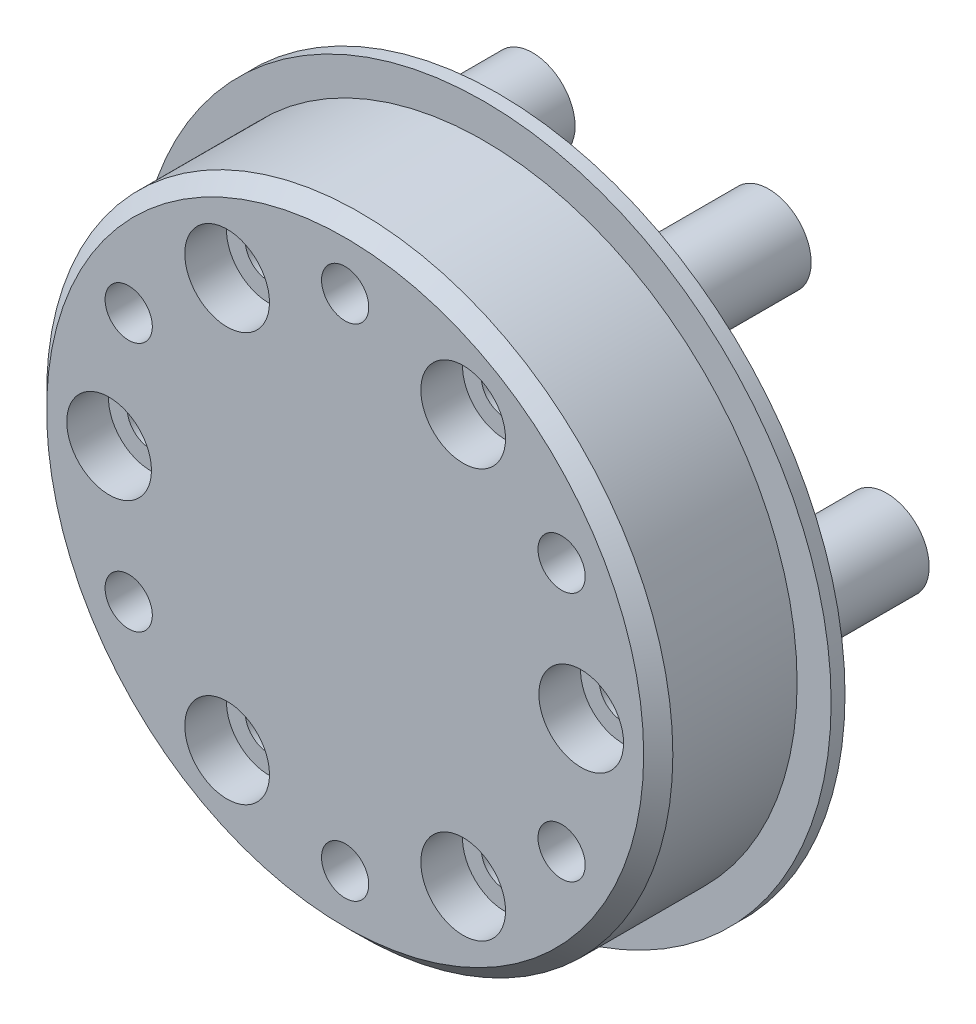
SolidWorks part; units mm, degrees
ref_plane "前视基准面" through (0, 0, 0) normal (0, 0, 1) x (1, 0, 0)
ref_plane "上视基准面" through (0, 0, 0) normal (0, 1, 0) x (1, 0, 0)
ref_plane "右视基准面" through (0, 0, 0) normal (1, 0, 0) x (0, 0, -1)
sketch "草图1" plane through (0, 0, 0) normal (0, 1, 0) x (1, 0, 0)
  line L0 (25, 11) -> (0, 11)
  line L1 (0, 11) -> (0, 10)
  line L2 (0, 10) -> (25, 10)
  line L3 (25, 10) -> (25, 11)
  line L4 (0, 11) -> (0, 10) construction
revolve "旋转1" add sketch "草图1" angle 360 about L4
sketch "草图2" plane through (0, 0, -10) normal (0, 0, 1) x (1, 0, 0)
  circle A0 centre (0, 0) radius 22.55
extrude "凸台-拉伸1" add sketch "草图2" along normal blind 10
ref_plane "基准面4" through (0, -14.7224, 0) normal (0, 1, 0) x (1, 0, 0)
sketch "草图3" plane through (0, -14.7224, 0) normal (0, 1, 0) x (1, 0, 0)
  line L0 (11.56, 22) -> (8.5, 22)
  line L1 (8.5, 22) -> (8.5, 11)
  line L2 (8.5, 11) -> (12.5, 11)
  line L3 (12.5, 11) -> (12.5, 12.5)
  line L4 (12.5, 12.5) -> (11.56, 12.5)
  line L5 (11.56, 12.5) -> (11.56, 22)
  line L6 (8.5, 22) -> (8.5, 11) construction
revolve "旋转2" add sketch "草图3" angle 360 about L6
sketch "草图4" plane through (0, -14.7224, 0) normal (0, 1, 0) x (1, 0, 0)
  line L0 (-5.44, 22) -> (-8.5, 22)
  line L1 (-8.5, 22) -> (-8.5, 11)
  line L2 (-8.5, 11) -> (-4.5, 11)
  line L3 (-4.5, 11) -> (-4.5, 12.5)
  line L4 (-4.5, 12.5) -> (-5.44, 12.5)
  line L5 (-5.44, 12.5) -> (-5.44, 22)
  line L6 (-8.5, 22) -> (-8.5, 11) construction
revolve "旋转3" add sketch "草图4" angle 360 about L6
sketch "草图5" plane through (0, 0, 0) normal (0, 1, 0) x (1, 0, 0)
  line L0 (-13.94, 22) -> (-17, 22)
  line L1 (-17, 22) -> (-17, 11)
  line L2 (-17, 11) -> (-13, 11)
  line L3 (-13, 11) -> (-13, 12.5)
  line L4 (-13, 12.5) -> (-13.94, 12.5)
  line L5 (-13.94, 12.5) -> (-13.94, 22)
  line L6 (-17, 22) -> (-17, 11) construction
revolve "旋转4" add sketch "草图5" angle 360 about L6
ref_plane "基准面5" through (0, 14.7224, 0) normal (0, 1, 0) x (1, 0, 0)
sketch "草图6" plane through (0, 14.7224, 0) normal (0, 1, 0) x (1, 0, 0)
  line L0 (-5.44, 22) -> (-8.5, 22)
  line L1 (-8.5, 22) -> (-8.5, 11)
  line L2 (-8.5, 11) -> (-4.5, 11)
  line L3 (-4.5, 11) -> (-4.5, 12.5)
  line L4 (-4.5, 12.5) -> (-5.44, 12.5)
  line L5 (-5.44, 12.5) -> (-5.44, 22)
  line L6 (-8.5, 22) -> (-8.5, 11) construction
revolve "旋转5" add sketch "草图6" angle 360 about L6
sketch "草图7" plane through (0, 14.7224, 0) normal (0, 1, 0) x (1, 0, 0)
  line L0 (11.56, 22) -> (8.5, 22)
  line L1 (8.5, 22) -> (8.5, 11)
  line L2 (8.5, 11) -> (12.5, 11)
  line L3 (12.5, 11) -> (12.5, 12.5)
  line L4 (12.5, 12.5) -> (11.56, 12.5)
  line L5 (11.56, 12.5) -> (11.56, 22)
  line L6 (8.5, 22) -> (8.5, 11) construction
revolve "旋转6" add sketch "草图7" angle 360 about L6
sketch "草图8" plane through (0, 0, 0) normal (0, 1, 0) x (1, 0, 0)
  line L0 (20.06, 22) -> (17, 22)
  line L1 (17, 22) -> (17, 11)
  line L2 (17, 11) -> (21, 11)
  line L3 (21, 11) -> (21, 12.5)
  line L4 (21, 12.5) -> (20.06, 12.5)
  line L5 (20.06, 12.5) -> (20.06, 22)
  line L6 (17, 22) -> (17, 11) construction
revolve "旋转7" add sketch "草图8" angle 360 about L6
hole_wizard "M3 六角头机械螺钉的柱形沉头孔1" positions "草图10" profile "草图9" counterbore size "M3" standard "ANSI Metric"
sketch "草图10" plane through (0, 0, -11) normal (0, 0, -1) x (-1, 0, 0)
  point P0 (15.5885, 9)
  point P1 (0, 18)
  point P2 (-15.5885, 9)
  point P3 (-15.5885, -9)
  point P4 (0, -18)
  point P5 (15.5885, -9)
sketch "草图9" plane through (-15.5885, 9, -11) normal (1, 0, 0) x (0, 1, 0)
  line L0 (0, 0) -> (0, 11)
  line L1 (0, 11) -> (1.7, 11)
  line L3 (1.7, 11) -> (1.7, 6)
  line L4 (1.7, 6) -> (2.25, 6)
  line L5 (2.25, 6) -> (2.25, 0)
  line L7 (2.25, 0) -> (0, 0)
  line L11 (0, -6.35) -> (0, 107.95) construction
  dimension "通孔孔直径" = 3.4
  dimension "通孔孔深度" = 11
  dimension "柱形沉头孔直径" = 4.5
  dimension "柱形沉头孔深度" = 6
hole_wizard "孔1" positions "草图12" profile "草图11" legacy
sketch "草图12" plane through (0, 0, -11) normal (0, 0, -1) x (-1, 0, 0)
  point P0 (0, 0)
sketch "草图11" plane through (0, 0, -11) normal (1, 0, 0) x (0, 1, 0)
  line L0 (0, 0) -> (0, 5)
  line L1 (0, 5) -> (4, 5)
  line L2 (4, 5) -> (4, 3)
  line L3 (4, 3) -> (5.08, 3)
  line L4 (5.08, 3) -> (5.08, 0)
  line L5 (5.08, 0) -> (0, 0)
  line L6 (0, 110) -> (0, -10) construction
  dimension "直径" = 8
  dimension "深度" = 5
  dimension "柱坑直径" = 10.16
  dimension "柱坑深度" = 3
hole_wizard "M3 六角头机械螺钉的柱形沉头孔2" positions "草图14" profile "草图13" counterbore size "M3" standard "ANSI Metric"
sketch "草图14" plane through (0, 0, 0) normal (0, 0, 1) x (1, 0, 0)
  point P0 (8.5, -14.7224)
  point P1 (-8.5, -14.7224)
  point P2 (-17, 0)
  point P3 (-8.5, 14.7224)
  point P4 (8.5, 14.7224)
  point P5 (17, 0)
sketch "草图13" plane through (8.5, -14.7224, 0) normal (1, 0, 0) x (0, -1, 0)
  line L0 (0, 0) -> (0, 22)
  line L1 (0, 22) -> (1.7, 22)
  line L3 (1.7, 22) -> (1.7, 3)
  line L4 (1.7, 3) -> (3.05, 3)
  line L5 (3.05, 3) -> (3.05, 0)
  line L7 (3.05, 0) -> (0, 0)
  line L11 (0, -6.35) -> (0, 107.95) construction
  dimension "通孔孔直径" = 3.4
  dimension "通孔孔深度" = 22
  dimension "柱形沉头孔直径" = 6.1
  dimension "柱形沉头孔深度" = 3
chamfer "倒角1" distance 1.05 angle 45 1 edges at (22.55, 0, 0)
